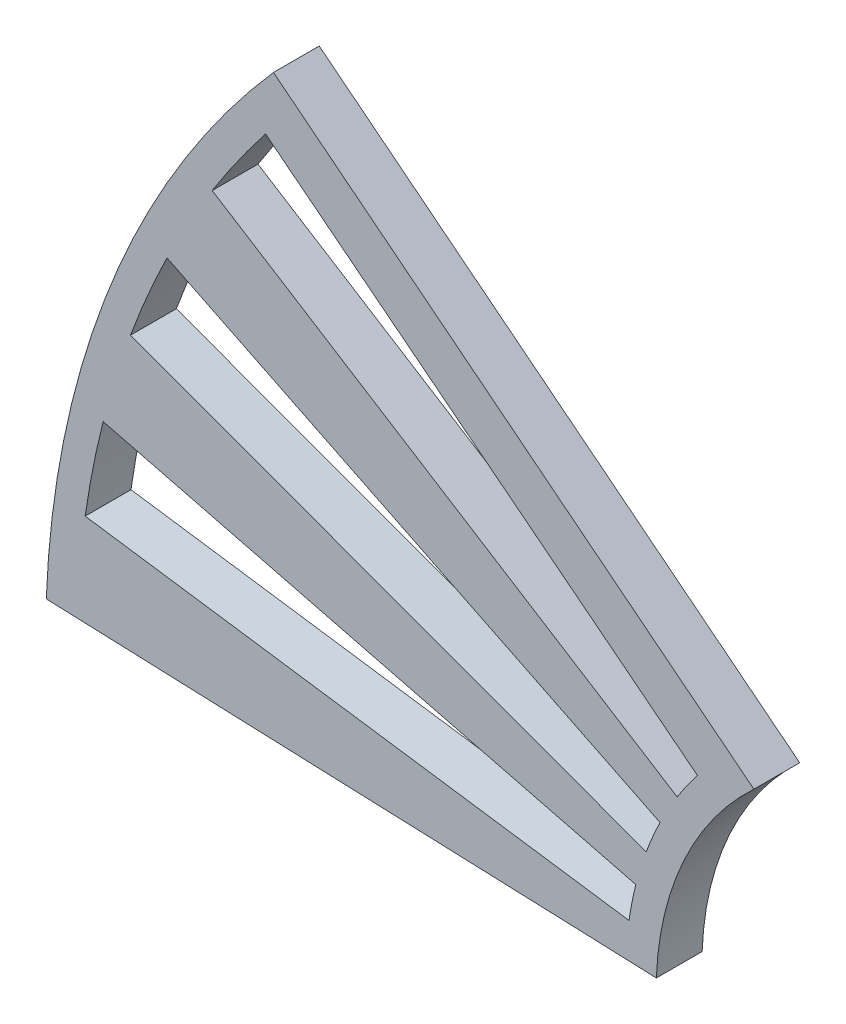
SolidWorks part; units mm, degrees
ref_plane "Front Plane" through (0, 0, 0) normal (0, 0, 1) x (1, 0, 0)
ref_plane "Top Plane" through (0, 0, 0) normal (0, 1, 0) x (1, 0, 0)
ref_plane "Right Plane" through (0, 0, 0) normal (1, 0, 0) x (0, 0, -1)
sketch "Sketch1" plane through (0, 0, 0) normal (0, 0, 1) x (1, 0, 0)
  line L0 (-19.9854, 0.7628) -> (-59.9563, 2.2884)
  line L2 (0, 0) -> (-50.7795, 31.96) construction
  line L3 (0, 0) -> (-57.3211, 17.7283) construction
  line L5 (-13.5925, 14.6712) -> (-45.0737, 39.6026)
  line L7 (-57.0177, 18.6812) -> (-57.0256, 18.6836)
  line L11 (-50.2398, 32.8019) -> (-50.2468, 32.8063)
  arc A0 (-45.0737, 39.6026) -> (-59.9563, 2.2884) centre (0, 0) ccw
  arc A1 (-13.5925, 14.6712) -> (-19.9854, 0.7628) centre (0, 0) ccw
  point P1 (0, 0)
  point P6 (-40.7774, 44.0137)
  point P9 (-40.8618, 41.162)
  point P10 (-57.8471, 4.2094)
  point P11 (-21.8167, 2.8342)
  point P12 (0, 0)
  point P13 (-16.3569, 14.7123)
  point P14 (0, 0)
  point P15 (0, 0)
  point P16 (0.2955, 0.9554)
  point P23 (0.5327, 0.8463)
  dimension "D1" = 120
  dimension "D2" = 40
  dimension "D4" = 15
  dimension "15" = 15
extrude "Boss-Extrude2" add sketch "Sketch1" along normal blind 3 contours L0 A0 L5 A1
sketch "Sketch2" plane through (0, 0, 3) normal (0, 0, 1) x (1, 0, 0)
  line L0 (0, 0) -> (-59.9563, 2.2884) construction
  line L1 (0, 0) -> (-58.1704, 14.704) construction
  line L2 (0, 0) -> (-53.8421, 26.477) construction
  line L3 (0, 0) -> (-47.1606, 37.0928) construction
  line L4 (0, 0) -> (-59.3887, 8.543) construction
  line L5 (0, 0) -> (-56.3147, 20.7039) construction
  line L6 (0, 0) -> (-50.7795, 31.96) construction
  line L7 (-45.5886, 35.8564) -> (-17.2922, 13.6007)
  line L8 (-18.6192, 11.7187) -> (-49.0869, 30.8947)
  line L9 (-52.0473, 25.5944) -> (-19.7421, 9.7082)
  line L10 (-20.6487, 7.5914) -> (-54.4376, 20.0138)
  line L11 (-56.2314, 14.2139) -> (-21.3291, 5.3915)
  line L12 (-21.7759, 3.1324) -> (-57.4091, 8.2583)
  circle A0 centre (0, 0) radius 22 construction
  circle A1 centre (0, 0) radius 58 construction
  arc A2 (-45.0737, 39.6026) -> (-59.9563, 2.2884) centre (0, 0) ccw construction
  arc A3 (-21.7759, 3.1324) -> (-21.3291, 5.3915) centre (0, 0) cw
  arc A4 (-20.6487, 7.5914) -> (-19.7421, 9.7082) centre (0, 0) cw
  arc A5 (-45.5886, 35.8564) -> (-49.0869, 30.8947) centre (0, 0) ccw
  arc A6 (-52.0473, 25.5944) -> (-54.4376, 20.0138) centre (0, 0) ccw
  arc A7 (-56.2314, 14.2139) -> (-57.4091, 8.2583) centre (0, 0) ccw
  arc A8 (-18.6192, 11.7187) -> (-17.2922, 13.6007) centre (0, 0) cw
  dimension "D1" = 116
  dimension "D2" = 44
  dimension "D3" = 12
  dimension "D4" = 12
  dimension "D5" = 12
  dimension "D6" = 6
  dimension "D7" = 6
  dimension "D8" = 6
extrude "Cut-Extrude1" cut sketch "Sketch2" against normal up to next
